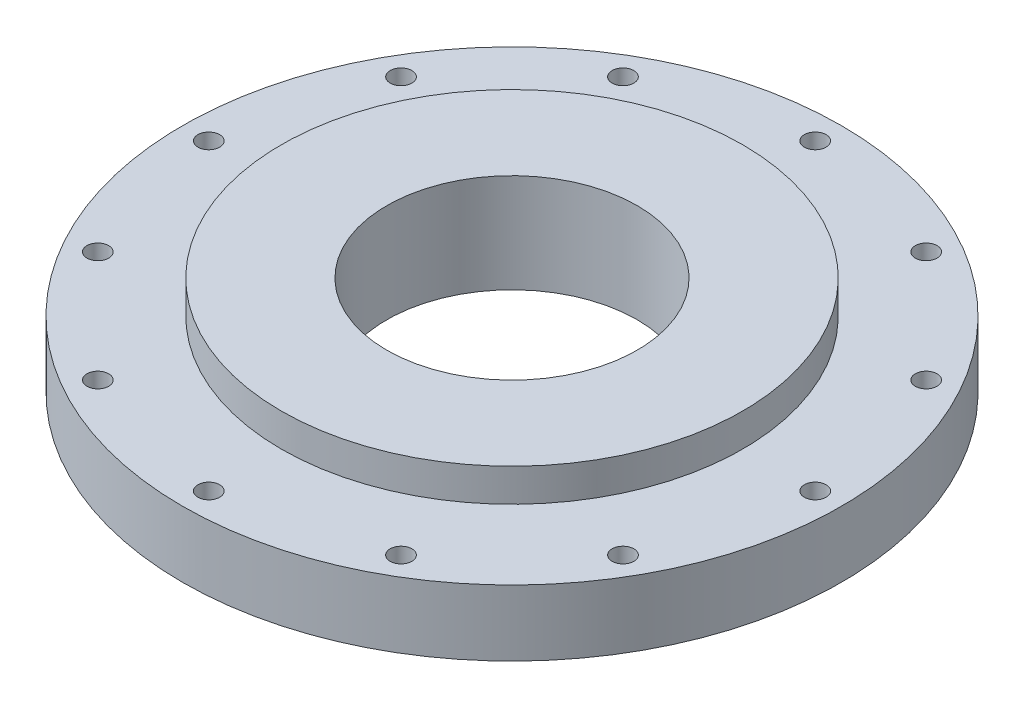
SolidWorks part; units mm, degrees
ref_plane "Front Plane" through (0, 0, 0) normal (0, 0, 1) x (1, 0, 0)
ref_plane "Top Plane" through (0, 0, 0) normal (0, 1, 0) x (1, 0, 0)
ref_plane "Right Plane" through (0, 0, 0) normal (1, 0, 0) x (0, 0, -1)
sketch "Sketch1" plane through (0, 0, 0) normal (0, 1, 0) x (1, 0, 0)
  circle A0 centre (0, 0) radius 63.5
  dimension "D1" = 127
extrude "Boss-Extrude1" add sketch "Sketch1" along normal blind 12.7 contours A0
sketch "Sketch2" plane through (0, 12.7, 0) normal (0, 1, 0) x (1, 0, 0)
  circle A0 centre (0, 0) radius 44.45
  dimension "D1" = 88.9
extrude "Boss-Extrude2" add sketch "Sketch2" along normal blind 6.35
sketch "Sketch3" plane through (0, 19.05, 0) normal (0, 1, 0) x (1, 0, 0)
  circle A0 centre (0, 0) radius 24.13
  dimension "D1" = 48.26
extrude "Cut-Extrude1" cut sketch "Sketch3" against normal through all both and the other way through all
sketch "Sketch4" plane through (0, 0, 0) normal (0, -1, 0) x (1, 0, 0)
  circle A0 centre (0, 0) radius 58.42 construction
  circle A1 centre (0, -58.42) radius 2.0955
  circle A2 centre (-29.21, -50.5932) radius 2.0955
  circle A3 centre (-50.5932, -29.21) radius 2.0955
  circle A4 centre (-58.42, 0) radius 2.0955
  circle A5 centre (-50.5932, 29.21) radius 2.0955
  circle A6 centre (-29.21, 50.5932) radius 2.0955
  circle A7 centre (0, 58.42) radius 2.0955
  circle A8 centre (29.21, 50.5932) radius 2.0955
  circle A9 centre (50.5932, 29.21) radius 2.0955
  circle A10 centre (58.42, 0) radius 2.0955
  circle A11 centre (50.5932, -29.21) radius 2.0955
  circle A12 centre (29.21, -50.5932) radius 2.0955
  point P29 (0, 0)
  dimension "D1" = 116.84
  dimension "D2" = 4.191
  dimension "D3" = 12
extrude "Cut-Extrude2" cut sketch "Sketch4" against normal through all
